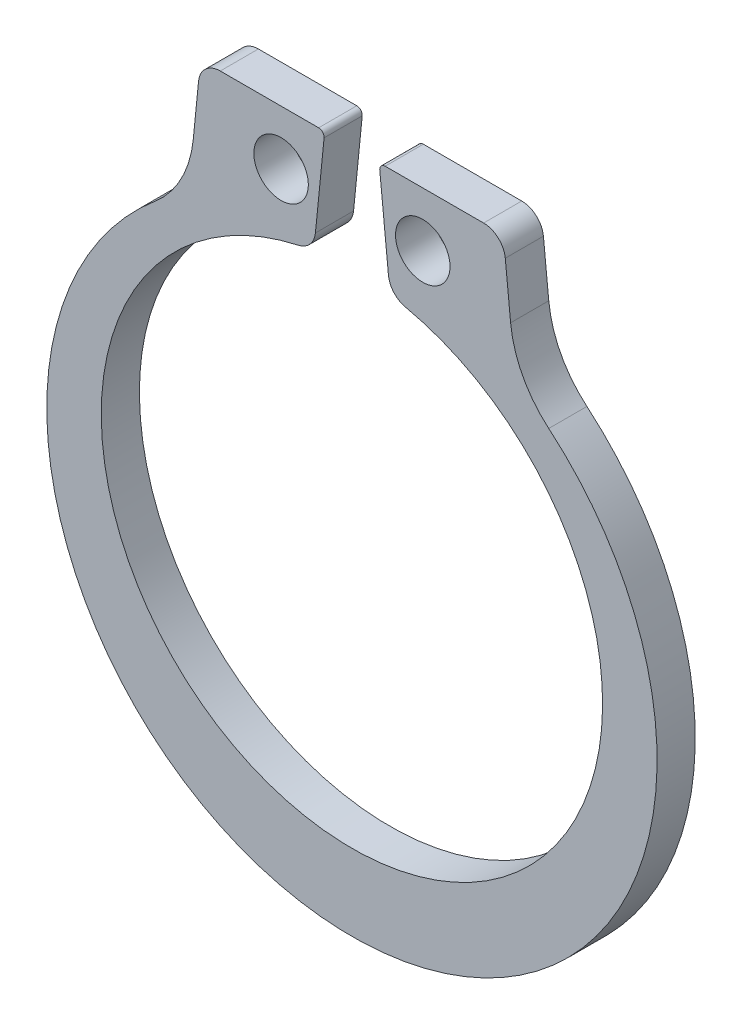
SolidWorks part; units mm, degrees
material "1023 Carbon Steel Sheet (SS)"
ref_plane "Front Plane" through (0, 0, 0) normal (0, 0, 1) x (1, 0, 0)
ref_plane "Top Plane" through (0, 0, 0) normal (0, 1, 0) x (1, 0, 0)
ref_plane "Right Plane" through (0, 0, 0) normal (1, 0, 0) x (0, 0, -1)
sketch "Sketch1" plane through (0, 0, 0) normal (0, 0, 1) x (1, 0, 0)
  line L0 (0, -0.508) -> (0, 0) construction
  line L1 (-3.6982, 6.6151) -> (-3.5741, 7.8565)
  line L2 (3.6982, 6.6151) -> (3.5741, 7.8565)
  line L3 (-3.0686, 8.314) -> (-0.7753, 8.314)
  line L4 (-0.649, 8.1743) -> (-0.8511, 6.1529)
  line L5 (3.0686, 8.314) -> (0.7753, 8.314)
  line L6 (0.649, 8.1743) -> (0.8511, 6.1529)
  line L7 (-0.635, 8.314) -> (0.635, 8.314) construction
  line L8 (0, 8.314) -> (0, 0) construction
  line L9 (-0.889, 5.774) -> (0.889, 5.774) construction
  line L10 (-1.651, 7.044) -> (1.651, 7.044) construction
  arc A0 (-1.2481, 5.7071) -> (1.2481, 5.7071) centre (0, 0) ccw
  arc A2 (-4.5873, 4.9268) -> (4.5873, 4.9268) centre (0, -0.508) ccw
  circle A3 centre (-1.651, 7.044) radius 0.635
  circle A4 centre (1.651, 7.044) radius 0.635
  arc A5 (4.5873, 4.9268) -> (3.6982, 6.6151) centre (6.2256, 6.8678) cw
  arc A6 (-4.5873, 4.9268) -> (-3.6982, 6.6151) centre (-6.2256, 6.8678) ccw
  arc A7 (3.0686, 8.314) -> (3.5741, 7.8565) centre (3.0686, 7.806) cw
  arc A8 (-3.0686, 8.314) -> (-3.5741, 7.8565) centre (-3.0686, 7.806) ccw
  arc A9 (0.8511, 6.1529) -> (1.2481, 5.7071) centre (1.3566, 6.2034) ccw
  arc A10 (-0.8511, 6.1529) -> (-1.2481, 5.7071) centre (-1.3566, 6.2034) cw
  arc A11 (0.7753, 8.314) -> (0.649, 8.1743) centre (0.7753, 8.187) ccw
  arc A12 (-0.7753, 8.314) -> (-0.649, 8.1743) centre (-0.7753, 8.187) cw
  point P18 (0, 7.044)
  point P26 (3.81, 5.4974)
  point P29 (-3.81, 5.4974)
  dimension "D1" = 11.684
  dimension "D2" = 14.224
  dimension "D9" = 1.27
  dimension "D10" = 1.27
  dimension "D5" = 2.54
  dimension "D14" = 0.508
  dimension "D15" = 0.127
  dimension "D3" = 0.508
  dimension "D4" = 3.81
  dimension "D6" = 1.27
  dimension "D7" = 2.54
  dimension "D8" = 1.778
  dimension "D11" = 1.27
  dimension "D12" = 3.302
  dimension "D13" = 3.81
extrude "Boss-Extrude1" add sketch "Sketch1" along normal blind 0.889
